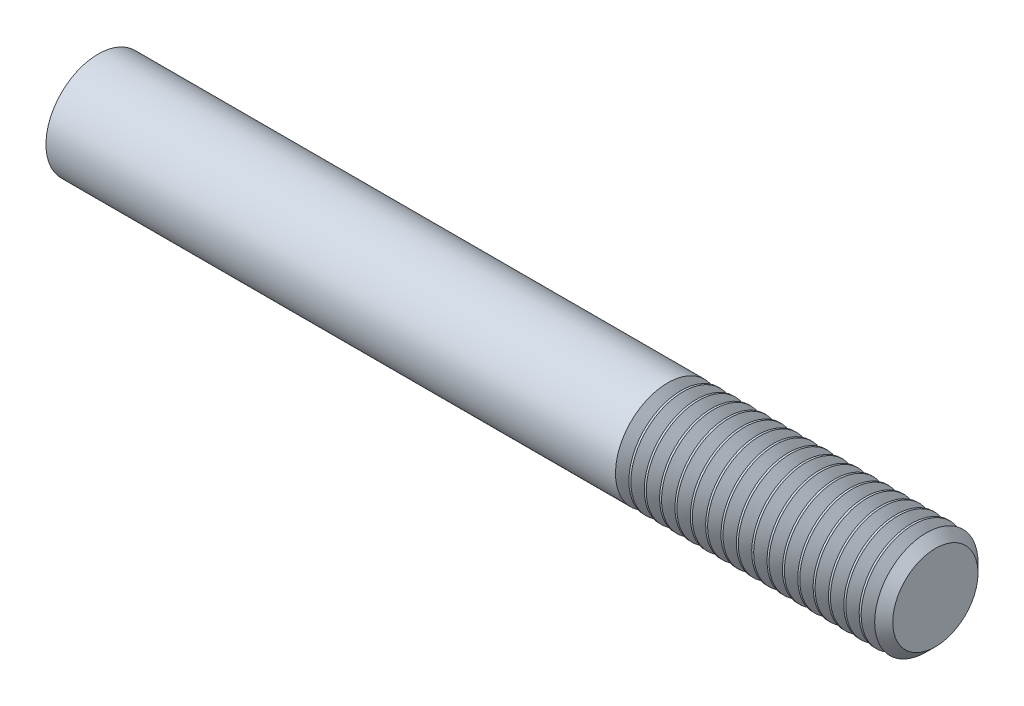
SolidWorks part; units mm, degrees
extrude "BaseHead" add sketch "Sketch1" along normal blind 0.254
sketch "Sketch1" plane through (0, 0, 0) normal (1, 0, 0) x (0, 0, -1)
  line L0 (6.35, 3.6662) -> (6.35, -3.6662)
  line L1 (-6.35, 3.6662) -> (-6.35, -3.6662)
  line L2 (6.35, -3.6662) -> (0, -7.3323)
  line L3 (0, -7.3323) -> (-6.35, -3.6662)
  line L4 (6.35, 3.6662) -> (0, 7.3323)
  line L5 (0, 7.3323) -> (-6.35, 3.6662)
  dimension "Width_flats" = 12.7
  dimension "D2" = 120
  dimension "D3" = 6.35
  dimension "D4" = 6.35
  dimension "D5" = 6.35
revolve "HeadChamfer" cut sketch "Sketch3" angle 360 about L6
sketch "Sketch3" plane through (0, 0, 0) normal (0, 0, 1) x (1, 0, 0)
  line L0 (0, 6.35) -> (4.2333, 13.6823)
  line L1 (0, 7.3323) -> (0, 3.6662) construction
  line L2 (4.2333, 13.6823) -> (4.2333, 20.0323)
  line L3 (4.2333, 20.0323) -> (-12.7, 20.0323)
  line L4 (-12.7, 20.0323) -> (-12.7, 6.35)
  line L5 (-12.7, 6.35) -> (0, 6.35)
  line L6 (0, 0) -> (99.06, 0) construction
  line L7 (0.254, 7.3323) -> (0, 7.3323) construction
  dimension "D4" = 6.35
  dimension "D1" = 6.35
  dimension "D2" = 6.35
  dimension "D3" = 12.7
  dimension "Head_ch_ang" = 30
ref_plane "Plane1" through (0, 0, 0) normal (0, 0, 1) x (1, 0, 0)
ref_plane "Plane2" through (0, 0, 0) normal (0, 1, 0) x (1, 0, 0)
ref_plane "Plane3" through (0, 0, 0) normal (1, 0, 0) x (0, 0, -1)
sketch "BodySke" plane through (0, 0, 0) normal (0, 0, 1) x (1, 0, 0)
  line L0 (0, 3.6662) -> (0, -3.6662) construction
  line L1 (0, 0) -> (101.854, 0)
  line L2 (0, 0) -> (0, 6.35)
  line L3 (0, 6.35) -> (100.6907, 6.35)
  line L4 (101.854, 0) -> (101.854, 5.1867)
  line L5 (0.254, 7.3323) -> (0.254, 3.6662) construction
  line L6 (101.854, 5.1867) -> (100.6907, 6.35)
  line L7 (0, 0) -> (96.52, 0) construction
  line L8 (101.854, -5.1867) -> (100.6907, -6.35) construction
  line L9 (0, -6.35) -> (100.6907, -6.35) construction
  line L10 (2.2073, 15.24) -> (2.2073, -1.27) construction
  line L11 (70.104, 15.24) -> (70.104, -1.27) construction
  line L12 (0.254, 3.6662) -> (0.254, -3.6662) construction
  dimension "Diameter" = 12.7
revolve "BaseBody" add sketch "BodySke" angle 360 about L7
cosmetic thread "ThreadCosmetic" [suppressed] parameters "Thread_length"=31.75, "Thread_minor"=10.3734
sketch "Sketch4" plane through (0, 0, 0) normal (0, 0, 1) x (1, 0, 0)
  line L1 (0.254, 7.3323) -> (0.254, 3.6662) construction
  line L2 (0.254, 6.35) -> (-0.127, 6.35)
  line L3 (0.254, 6.35) -> (0.254, 32.7323)
  line L4 (0.254, 32.7323) -> (-0.127, 32.7323)
  line L5 (0, 0) -> (95.25, 0) construction
  line L6 (0, 0) -> (96.52, 0) construction
  line L7 (-0.127, 6.35) -> (-0.127, 32.7323)
  line L8 (0.5672, 7.3323) -> (0.254, 7.3323) construction
  dimension "D1" = 6.35
  dimension "D2" = 25.4
revolve "BearingFace" cut sketch "Sketch4" angle 360 about L5
sketch "ThdSchSke" plane through (0, 0, 0) normal (0, 0, 1) x (1, 0, 0)
  line L0 (70.104, -5.1867) -> (69.2894, -6.35)
  line L1 (70.104, -5.1867) -> (70.9186, -6.35)
  line L2 (70.9186, -6.35) -> (70.9186, -7.9375)
  line L3 (-3.175, 0) -> (5.1513, 0) construction
  line L5 (70.9186, -7.9375) -> (69.2894, -7.9375)
  line L6 (69.2894, -7.9375) -> (69.2894, -6.35)
  dimension "Thread_minor" = 10.3734
  dimension "Diameter" = 12.7
  dimension "Start" = 70.104
revolve "ThreadSchematic" cut sketch "ThdSchSke" angle 360 about L3
pattern_linear "ThdSchPat" count 17 spacing 1.8676 along (1, 0, 0) of "ThreadSchematic"
sketch "Croquis1" plane through (0, 0, 0) normal (-1, 0, 0) x (0, 0, 1)
  line L0 (-1.905, 2.54) -> (1.905, 2.54)
  arc A0 (-1.905, 2.54) -> (1.905, 2.54) centre (0, 0) ccw
  dimension "D1" = 6.35
  dimension "D2" = 2.54
extrude "Cortar-Extruir1" cut sketch "Croquis1" against normal blind 53.34
equation "\"D3@Sketch1\" = \"Width_flats@Sketch1\" / 2"
equation "\"D4@Sketch1\" = \"D3@Sketch1\""
equation "\"D5@Sketch1\" = \"D4@Sketch1\""
equation "\"Thread_minor@ThreadCosmetic\" = \"Minor_dia@BodySke\""
equation "\"D1@Sketch3\" = \"Width_flats@Sketch1\" / 2"
equation "\"D1@Sketch4\" = \"Width_flats@Sketch1\" / 2"
equation "\"Thread_length@ThreadCosmetic\" = ((sgn( (\"Length@BodySke\" - \"Advance@BodySke\" ) - \"Thread_nom@BodySke\" )-1)*( (\"Length@BodySke\" - \"Advance@BodySke\" ) - \"Thread_nom@BodySke\" ))/-2+ \"Thread_nom@BodySke\""
equation "\"Thread_minor@ThdSchSke\" = \"Minor_dia@BodySke\""
equation "\"Diameter@ThdSchSke\" = \"Diameter@BodySke\""
equation "\"Overcut@ThdSchSke\" = \"Diameter@BodySke\" * 1.25"
equation "\"Start@ThdSchSke\" = \"Head_ht@BaseHead\" + \"Length@BodySke\" - \"Thread_length@ThreadCosmetic\"  '---Non-countersunk---"
equation "\"Num_threads@ThdSchPat\" = int( \"Thread_length@ThreadCosmetic\" / \"Advance@BodySke\" + 0.999 )  + 1"
equation "\"Advance@ThdSchPat\" = \"Thread_length@ThreadCosmetic\" /  (\"Num_threads@ThdSchPat\" - 1) 'relax it"
equation "\"Num_threads@ThdSchPat\" = \"Num_threads@ThdSchPat\" - sgn( \"Num_threads@ThdSchPat\" - 1) '---chamfered tips only---"
